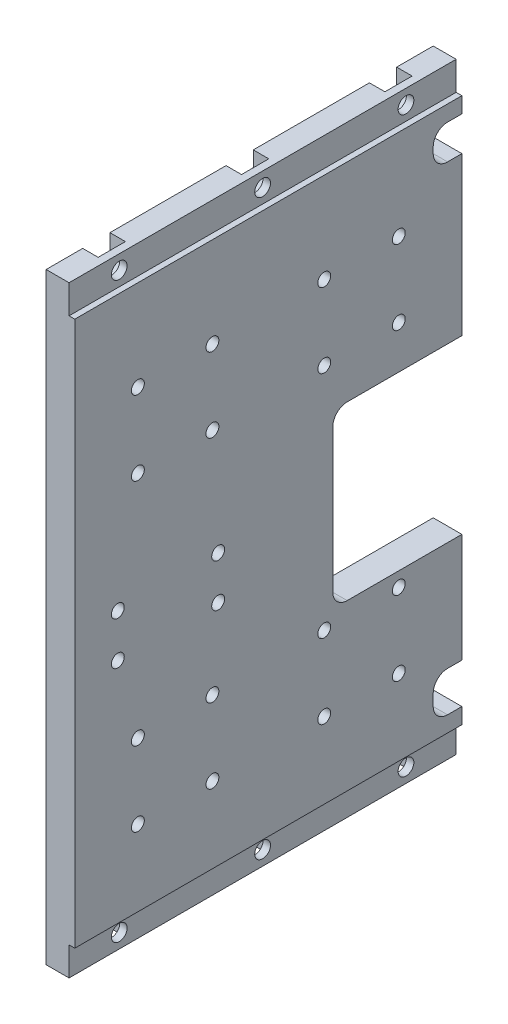
SolidWorks part; units mm, degrees
ref_plane "Front" through (0, 0, 0) normal (0, 0, 1) x (1, 0, 0)
ref_plane "Top" through (0, 0, 0) normal (0, 1, 0) x (1, 0, 0)
ref_plane "Right" through (0, 0, 0) normal (1, 0, 0) x (0, 0, -1)
sketch "Sketch1" plane through (0, 0, 0) normal (1, 0, 0) x (0, 0, -1)
  line L2 (0, 210) -> (135, 210)
  line L3 (0, 210) -> (0, 0)
  line L4 (0, 0) -> (135, 0)
  line L5 (135, 210) -> (135, 0)
  dimension "D1" = 210
  dimension "D2" = 135
extrude "Boss-Extrude1" add sketch "Sketch1" along normal blind 10
sketch "Sketch2" plane through (10, 0, 0) normal (1, 0, 0) x (0, 0, -1)
  line L0 (135, 0) -> (135, 210) construction
  line L1 (90, 127.5) -> (135, 127.5)
  line L2 (90, 127.5) -> (90, 67.5)
  line L3 (90, 67.5) -> (135, 67.5)
  line L4 (135, 127.5) -> (135, 67.5)
  line L5 (0, 0) -> (135, 0) construction
  dimension "D1" = 90
  dimension "D2" = 67.5
  dimension "D3" = 60
extrude "Cut-Extrude1" cut sketch "Sketch2" against normal through all
sketch "Sketch3" plane through (10, 0, 0) normal (1, 0, 0) x (0, 0, -1)
  line L0 (135, 0) -> (135, 67.5) construction
  line L1 (125, 29.5) -> (135, 29.5)
  line L2 (125, 29.5) -> (125, 15.5)
  line L3 (125, 15.5) -> (135, 15.5)
  line L4 (135, 29.5) -> (135, 15.5)
  line L5 (125, 194.5) -> (135, 194.5)
  line L6 (125, 194.5) -> (125, 182.5)
  line L7 (125, 182.5) -> (135, 182.5)
  line L8 (135, 194.5) -> (135, 182.5)
  line L9 (135, 127.5) -> (135, 210) construction
  dimension "D1" = 15.5
  dimension "D2" = 14
  dimension "D3" = 153
  dimension "D4" = 12
  dimension "D5" = 125
extrude "Cut-Extrude2" cut sketch "Sketch3" against normal through all
sketch "Sketch4" plane through (10, 0, 0) normal (1, 0, 0) x (0, 0, -1)
  line L0 (135, 0) -> (135, 15.5) construction
  line L1 (0, 0) -> (135, 0)
  line L2 (0, 0) -> (0, 10)
  line L3 (0, 10) -> (135, 10)
  line L4 (135, 0) -> (135, 10)
  line L5 (135, 194.5) -> (135, 210) construction
  line L6 (0, 210) -> (135, 210)
  line L7 (0, 210) -> (0, 200)
  line L8 (0, 200) -> (135, 200)
  line L9 (135, 210) -> (135, 200)
  dimension "D1" = 10
  dimension "D2" = 190
extrude "Cut-Extrude3" cut sketch "Sketch4" against normal blind 2
sketch "Sketch5" plane through (0, 0, 0) normal (-1, 0, 0) x (0, 0, 1)
  line L0 (0, 210) -> (0, 0) construction
  line L1 (0, 0) -> (-135, 0) construction
  circle A0 centre (-35, 175) radius 2.5
  circle A1 centre (-100, 175) radius 2.5
  dimension "D1" = 5
  dimension "D2" = 175
  dimension "D3" = 65
  dimension "D4" = 35
extrude "Cut-Extrude4" cut sketch "Sketch5" against normal blind 6
sketch "Sketch6" plane through (0, 0, 0) normal (-1, 0, 0) x (0, 0, 1)
  line L0 (-22.25, 5) -> (-22.25, 0)
  line L1 (-12.75, 5) -> (-12.75, 0)
  line L2 (-22.25, 0) -> (-12.75, 0)
  line L3 (0, 0) -> (-135, 0) construction
  line L4 (-22.25, 205) -> (-22.25, 210)
  line L5 (-12.75, 205) -> (-12.75, 210)
  line L6 (-22.25, 210) -> (-12.75, 210)
  line L7 (-135, 210) -> (0, 210) construction
  arc A0 (-12.75, 5) -> (-22.25, 5) centre (-17.5, 5) ccw
  arc A1 (-22.25, 205) -> (-12.75, 205) centre (-17.5, 205) ccw
  dimension "D1" = 9.5
  dimension "D2" = 5
  dimension "D3" = 17.5
  dimension "D4" = 205
extrude "Cut-Extrude5" cut sketch "Sketch6" against normal blind 5.4
pattern_linear "LPattern1" count 3 spacing 50 along (0, 0, -1) of "Cut-Extrude5"
hole_wizard "Ø5.5 (5.5) Diameter Hole1" positions "Sketch14" profile "Sketch13" hole size "Ø5.5" standard "JIS" end condition through all
sketch "Sketch14" plane through (5.4, 0, 0) normal (-1, 0, 0) x (0, 0, 1)
  point P0 (-17.5, 205)
  point P17 (-17.5, 5)
sketch "Sketch13" plane through (5.4, 205, -17.5) normal (0, 1, 0) x (0, 0, 1)
  line L0 (0, 0) -> (0, 4.6)
  line L1 (0, 4.6) -> (2.75, 4.6)
  line L2 (2.75, 4.6) -> (2.75, 0)
  line L5 (2.75, 0) -> (0, 0)
  line L11 (0, -6.35) -> (0, 107.95) construction
  dimension "Thru Hole Dia." = 5.5
  dimension "Thru Hole Depth" = 4.6
pattern_linear "LPattern3" count 3 spacing 50 along (0, 0, -1) of "Ø5.5 (5.5) Diameter Hole1"
hole_wizard "Ø4.5 (4.5) Diameter Hole1" positions "Sketch9" profile "Sketch8" hole size "Ø4.5" standard "JIS" end condition through all
sketch "Sketch9" plane through (10, 0, 0) normal (1, 0, 0) x (0, 0, -1)
  point P0 (15, 104.4)
  point P1 (50, 104.4)
  point P3 (15, 89.4)
  point P5 (50, 89.4)
  dimension "D1" = 89.4
  dimension "D2" = 15
  dimension "D3" = 15
  dimension "D4" = 35
sketch "Sketch8" plane through (10, 104.4, -15) normal (0, 1, 0) x (0, 0, -1)
  line L0 (0, 0) -> (0, 10)
  line L1 (0, 10) -> (2.25, 10)
  line L2 (2.25, 10) -> (2.25, 0)
  line L5 (2.25, 0) -> (0, 0)
  line L11 (0, -6.35) -> (0, 107.95) construction
  dimension "Thru Hole Dia." = 4.5
  dimension "Thru Hole Depth" = 10
hole_wizard "Ø4.5 (4.5) Diameter Hole2" positions "Sketch11" profile "Sketch10" hole size "Ø4.5" standard "JIS" end condition through all
sketch "Sketch11" plane through (10, 0, 0) normal (1, 0, 0) x (0, 0, -1)
  point P0 (22, 36.5)
  point P4 (22, 62.5)
  point P6 (48, 62.5)
  point P8 (48, 36.5)
  dimension "D1" = 22
  dimension "D2" = 36.5
  dimension "D3" = 26
  dimension "D4" = 26
sketch "Sketch10" plane through (10, 36.5, -22) normal (0, 1, 0) x (0, 0, -1)
  line L0 (0, 0) -> (0, 10)
  line L1 (0, 10) -> (2.25, 10)
  line L2 (2.25, 10) -> (2.25, 0)
  line L5 (2.25, 0) -> (0, 0)
  line L11 (0, -6.35) -> (0, 107.95) construction
  dimension "Thru Hole Dia." = 4.5
  dimension "Thru Hole Depth" = 10
pattern_linear "LPattern2" count 2 spacing 65 along (0, 0, -1) count 2 spacing 106 along (0, 1, 0) of "Ø4.5 (4.5) Diameter Hole2"
fillet "Fillet1" radius 5 6 edges at (5, 194.5, -125) (5, 182.5, -125) (5, 127.5, -90) (5, 67.5, -90) (5, 15.5, -125) (5, 29.5, -125)
